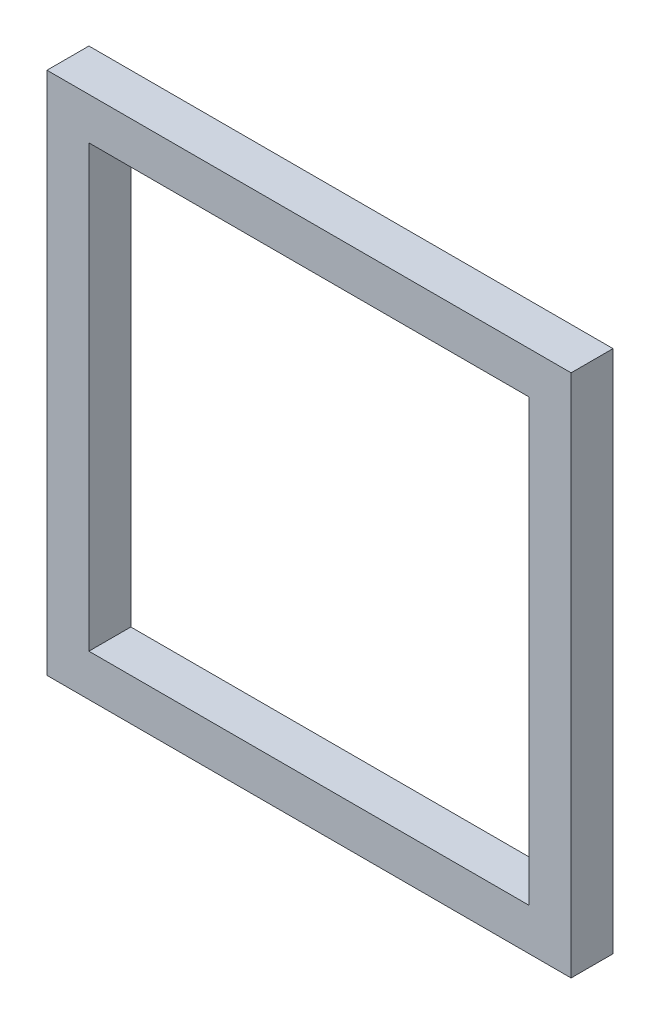
SolidWorks part; units mm, degrees
ref_plane "Front Plane" through (0, 0, 0) normal (0, 0, 1) x (1, 0, 0)
ref_plane "Top Plane" through (0, 0, 0) normal (0, 1, 0) x (1, 0, 0)
ref_plane "Right Plane" through (0, 0, 0) normal (1, 0, 0) x (0, 0, -1)
sketch "Sketch1" plane through (0, 0, 0) normal (0, 0, 1) x (1, 0, 0)
  line L1 (-23.7059, 14.4853) -> (26.2941, 14.4853)
  line L2 (-23.7059, 14.4853) -> (-23.7059, -35.5147)
  line L3 (-23.7059, -35.5147) -> (26.2941, -35.5147)
  line L4 (26.2941, 14.4853) -> (26.2941, -35.5147)
  line L5 (-19.7059, 10.4853) -> (22.2941, 10.4853)
  line L6 (-19.7059, 10.4853) -> (-19.7059, -31.5147)
  line L7 (-19.7059, -31.5147) -> (22.2941, -31.5147)
  line L8 (22.2941, 10.4853) -> (22.2941, -31.5147)
  dimension "D1" = 50
  dimension "D2" = 50
  dimension "D3" = 4
  dimension "D4" = 4
  dimension "D5" = 4
  dimension "D6" = 4
extrude "Boss-Extrude1" add sketch "Sketch1" along normal blind 4
